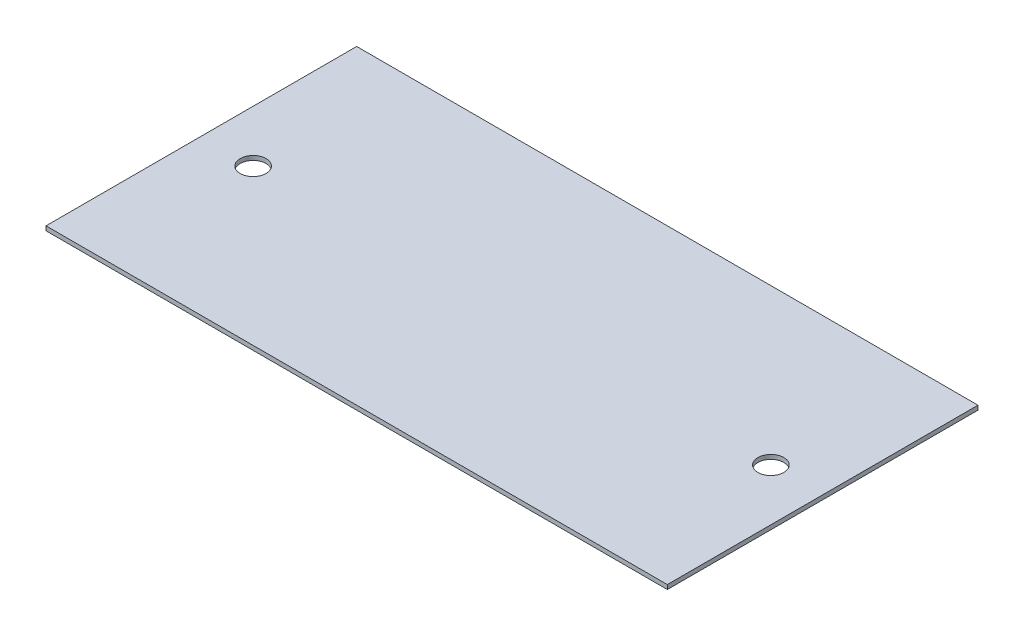
SolidWorks part; units mm, degrees
ref_plane "Front Plane" through (0, 0, 0) normal (0, 0, 1) x (1, 0, 0)
ref_plane "Top Plane" through (0, 0, 0) normal (0, 1, 0) x (1, 0, 0)
ref_plane "Right Plane" through (0, 0, 0) normal (1, 0, 0) x (0, 0, -1)
sketch "Sketch1" plane through (0, 0, 0) normal (0, 1, 0) x (1, 0, 0)
  line L1 (0, 0) -> (914.4, 0)
  line L2 (0, 0) -> (0, 457.2)
  line L3 (0, 457.2) -> (914.4, 457.2)
  line L4 (914.4, 0) -> (914.4, 457.2)
  line L5 (0, 0) -> (914.4, 457.2) construction
  line L6 (0, 457.2) -> (914.4, 0) construction
  point P0 (0, 0)
  dimension "D1" = 457.2
  dimension "D2" = 914.4
extrude "Boss-Extrude1" add sketch "Sketch1" along normal blind 6.35
sketch "Sketch2" plane through (0, 6.35, 0) normal (0, 1, 0) x (1, 0, 0)
  line L0 (0, 228.6) -> (914.4, 228.6) construction
  line L1 (914.4, 457.2) -> (0, 457.2) construction
  line L2 (457.2, 457.2) -> (457.2, 0) construction
  line L3 (0, 457.2) -> (0, 0) construction
  line L4 (76.2, 457.2) -> (76.2, 0)
  line L5 (76.2, 457.2) -> (76.2, 0) construction
  line L6 (838.2, 457.2) -> (838.2, 0) construction
  circle A0 centre (76.2, 228.6) radius 19.05
  circle A1 centre (838.2, 228.6) radius 19.05
  dimension "D3" = 38.1
  dimension "D1" = 228.6
  dimension "D4" = 457.2
  dimension "D2" = 76.2
extrude "Cut-Extrude1" cut sketch "Sketch2" against normal through all
